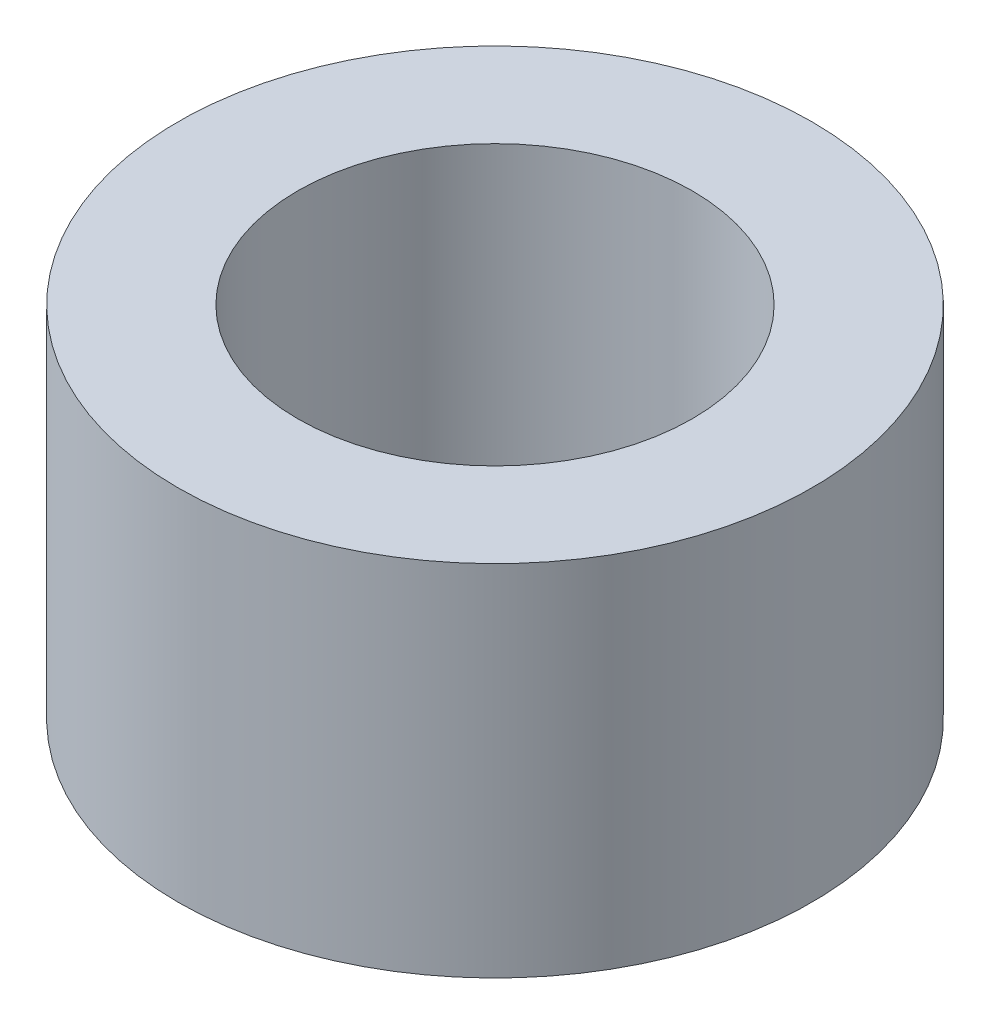
SolidWorks part; units mm, degrees
ref_plane "Front Plane" through (0, 0, 0) normal (0, 0, 1) x (1, 0, 0)
ref_plane "Top Plane" through (0, 0, 0) normal (0, 1, 0) x (1, 0, 0)
ref_plane "Right Plane" through (0, 0, 0) normal (1, 0, 0) x (0, 0, -1)
sketch "Sketch1" plane through (0, 0, 0) normal (0, 1, 0) x (1, 0, 0)
  circle A0 centre (0, 0) radius 3.3
  circle A1 centre (0, 0) radius 5.3
  point P5 (0, 0)
  dimension "D1" = 6.6
  dimension "D2" = 10.6
extrude "Boss-Extrude1" add sketch "Sketch1" along normal blind 6
